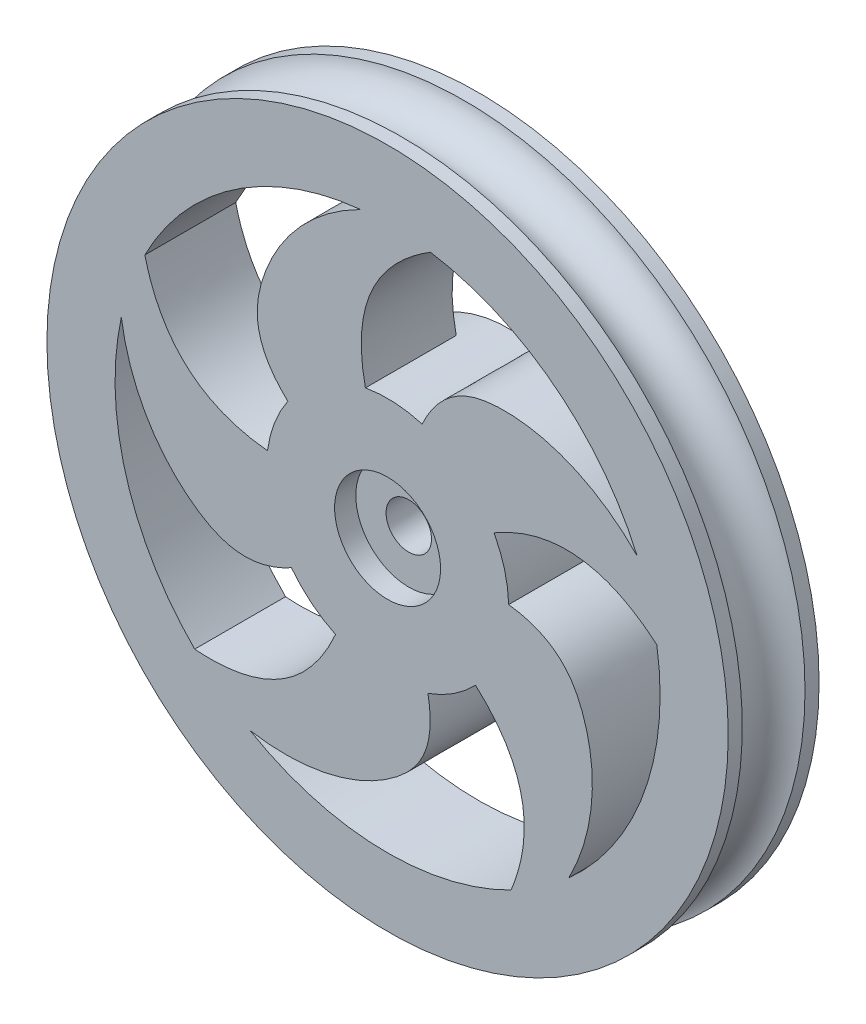
SolidWorks part; units mm, degrees
ref_plane "Front Plane" through (0, 0, 0) normal (0, 0, 1) x (1, 0, 0)
ref_plane "Top Plane" through (0, 0, 0) normal (0, 1, 0) x (1, 0, 0)
ref_plane "Right Plane" through (0, 0, 0) normal (1, 0, 0) x (0, 0, -1)
sketch "Sketch1" plane through (0, 0, 0) normal (0, 0, 1) x (1, 0, 0)
  circle A0 centre (0, 0) radius 28.575
  dimension "2.25" = 57.15
extrude "Boss-Extrude1" add sketch "Sketch1" along normal blind 7.62
sketch "Sketch3" plane through (0, 0, 0) normal (1, 0, 0) x (0, 0, -1)
  line L1 (0, -28.575) -> (0, 28.575) construction
  circle A0 centre (-3.81, 29.0125) radius 2.667
  dimension "0.21" = 5.334
  dimension "0.2" = 3.81
ref_axis "Axis1" through (0, 0, 0) along (0, 0, 1)
revolve "Cut-Revolve1" cut sketch "Sketch3" angle 360 about axis through (0, 0, 0) along (0, 0, 1)
sketch "Sketch4" plane through (0, 0, 0) normal (0, 0, -1) x (-1, 0, 0)
  line L1 (7.0209, 2.976) -> (0.9331, 7.5683)
  line L2 (0.9331, 7.5683) -> (-6.0878, 4.5923)
  line L3 (-6.0878, 4.5923) -> (-7.0209, -2.976)
  line L4 (-7.0209, -2.976) -> (-0.9331, -7.5683)
  line L5 (-0.9331, -7.5683) -> (6.0878, -4.5923)
  line L6 (6.0878, -4.5923) -> (7.0209, 2.976)
  circle A0 centre (0, 0) radius 6.604 construction
sketch "Sketch5" plane through (0, 0, 0) normal (0, 0, -1) x (-1, 0, 0)
  circle A0 centre (0, 0) radius 10.16
  dimension "0.85" = 20.32
extrude "Boss-Extrude3" add sketch "Sketch5" along normal blind 2.54
extrude "Cut-Extrude1" cut sketch "Sketch4" along normal blind 2.54 and the other way blind 2.54
sketch "Sketch6" plane through (0, 0, 7.62) normal (0, 0, 1) x (1, 0, 0)
  circle A0 centre (0, 0) radius 1.905
  dimension "0.12" = 3.81
extrude "Cut-Extrude2" cut sketch "Sketch6" against normal through all
sketch "Sketch7" plane through (0, 0, 0) normal (0, 0, -1) x (-1, 0, 0)
  arc A0 (20.3583, 10.398) -> (2.2627, 22.7477) centre (0, 0) ccw
  circle A1 centre (0, 0) radius 10.16 construction
  arc A2 (10.0742, 1.3175) -> (8.3678, 5.7625) centre (0, 0) ccw
  arc A3 (16.1801, -16.1488) -> (22.3336, 4.8775) centre (0, 0) ccw
  arc A4 (4.3661, -9.174) -> (8.0662, -6.1775) centre (0, 0) ccw
  arc A5 (-10.3585, -20.3785) -> (11.5402, -19.7333) centre (0, 0) ccw
  arc A6 (-7.3758, -6.9873) -> (-3.3826, -9.5804) centre (0, 0) ccw
  arc A7 (-22.582, 3.5542) -> (-15.2014, -17.0733) centre (0, 0) ccw
  arc A8 (-8.9246, 4.8556) -> (-10.1568, 0.2565) centre (0, 0) ccw
  arc A9 (-3.598, 22.5751) -> (-20.9352, 9.1814) centre (0, 0) ccw
  arc A10 (1.8601, 9.9883) -> (-2.8946, 9.7389) centre (0, 0) ccw
  spline S0 degree 3 poles (2.2627, 22.7477) (6.4057, 20.6851) (11.1771, 15.1021) (11.3303, 8.5335) (8.3678, 5.7625) knots 0 0 0 0 0.593727 1 1 1 1
  spline S1 degree 2 poles (20.3583, 10.398) (18.3576, 2.1492) (10.0742, 1.3175) knots 0 0 0 1 1 1
  spline S2 degree 3 poles (22.3336, 4.8775) (21.6522, 0.2998) (17.8169, -5.9632) (11.6171, -8.1388) (8.0662, -6.1775) knots 0 0 0 0 0.593727 1 1 1 1
  spline S3 degree 2 poles (16.1801, -16.1488) (7.7168, -16.795) (4.3661, -9.174) knots 0 0 0 1 1 1
  spline S4 degree 3 poles (11.5402, -19.7333) (6.9761, -20.4998) (-0.1657, -18.7876) (-4.1506, -13.5636) (-3.3826, -9.5804) knots 0 0 0 0 0.593727 1 1 1 1
  spline S5 degree 2 poles (-10.3585, -20.3785) (-13.5883, -12.5291) (-7.3758, -6.9873) knots 0 0 0 1 1 1
  spline S6 degree 3 poles (-15.2014, -17.0733) (-17.3408, -12.9694) (-17.9192, -5.6481) (-14.1823, -0.244) (-10.1568, 0.2565) knots 0 0 0 0 0.593727 1 1 1 1
  spline S7 degree 2 poles (-22.582, 3.5542) (-16.1149, 9.0516) (-8.9246, 4.8556) knots 0 0 0 1 1 1
  spline S8 degree 3 poles (-20.9352, 9.1814) (-17.6932, 12.4843) (-10.909, 15.2968) (-4.6146, 13.4128) (-2.8946, 9.7389) knots 0 0 0 0 0.593727 1 1 1 1
  spline S9 degree 2 poles (-3.598, 22.5751) (3.6288, 18.1232) (1.8601, 9.9883) knots 0 0 0 1 1 1
  point P37 (0, 0)
  dimension "D1" = 45.72
  dimension "D2" = 5
extrude "Cut-Extrude3" cut sketch "Sketch7" against normal through all
sketch "Sketch8" plane through (0, 0, 7.62) normal (0, 0, 1) x (1, 0, 0)
  circle A0 centre (0, 0) radius 4.445
  dimension "D1" = 8.89
extrude "Cut-Extrude4" cut sketch "Sketch8" against normal blind 1.778
